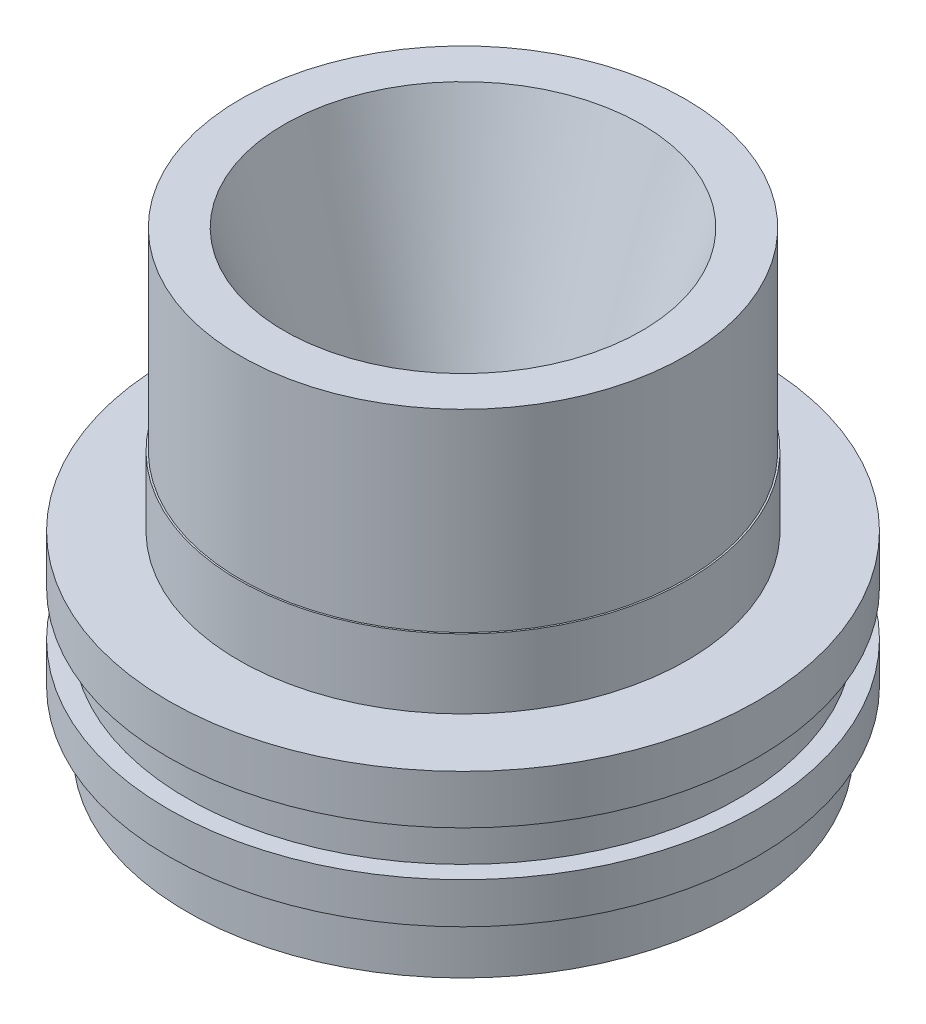
SolidWorks part; units mm, degrees
material "Graphite AR-12"
ref_plane "Front Plane" through (0, 0, 0) normal (0, 0, 1) x (1, 0, 0)
ref_plane "Top Plane" through (0, 0, 0) normal (0, 1, 0) x (1, 0, 0)
ref_plane "Right Plane" through (0, 0, 0) normal (1, 0, 0) x (0, 0, -1)
sketch "Sketch1" plane through (0, 0, 0) normal (0, 0, 1) x (1, 0, 0)
  line L0 (0, 0) -> (0, 12.9027) construction
  line L1 (0, 12.9027) -> (-27.8338, 12.9027) construction
  line L2 (-27.8338, 12.9027) -> (-13.589, -31.3695)
  line L3 (-13.589, -31.3695) -> (-13.589, -44.0695)
  line L4 (-40.513, -57.9125) -> (-42.926, -57.9125)
  line L5 (-42.926, -57.9125) -> (-42.926, -48.9463)
  line L6 (-42.926, -48.9463) -> (-45.847, -48.9463)
  line L7 (-45.847, -48.9463) -> (-45.847, -42.5963)
  line L8 (-45.847, -42.5963) -> (-42.926, -42.5963)
  line L9 (-42.926, -42.5963) -> (-42.926, -35.6113)
  line L10 (-45.847, -27.9913) -> (-34.8996, -27.9913)
  line L11 (-34.8996, -27.9913) -> (-34.8996, -17.1963)
  line L12 (-34.6456, -17.1963) -> (-34.6456, 12.9027)
  line L13 (-34.6456, 12.9027) -> (-27.8338, 12.9027)
  line L14 (-13.589, -44.0695) -> (-40.513, -57.9125)
  line L15 (-42.926, -35.6113) -> (-45.847, -35.6113)
  line L16 (-45.847, -35.6113) -> (-45.847, -27.9913)
  line L19 (-34.8996, -17.1963) -> (-34.6456, -17.1963)
  dimension "D2" = 12.7
  dimension "D3" = 13.843
  dimension "D4" = 13.589
  dimension "D5" = 8.9662
  dimension "D6" = 6.35
  dimension "D7" = 10.795
  dimension "D8" = 7.62
  dimension "D9" = 10.9474
  dimension "D10" = 2.413
  dimension "D11" = 30.099
  dimension "D12" = 20.955
  dimension "D13" = 0.254
  dimension "D14" = 42.926
  dimension "D15" = 45.847
revolve "Revolve1" add sketch "Sketch1" angle 360 about L0
sketch "Sketch2" plane through (0, 12.9027, 0) normal (0, 1, 0) x (1, 0, 0)
  point P0 (0, 0)
